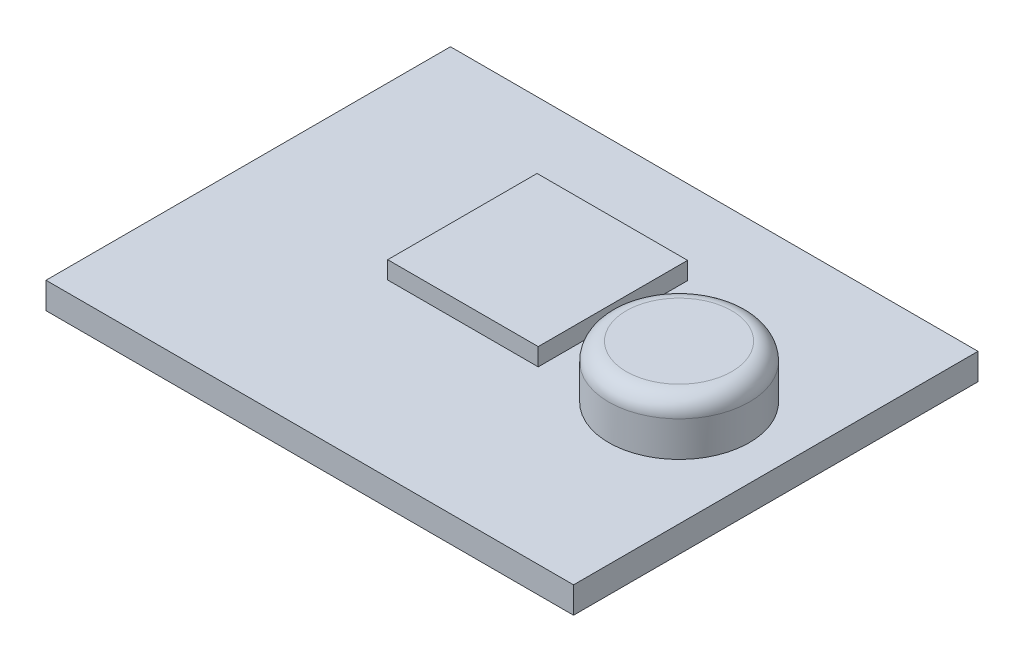
SolidWorks part; units mm, degrees
ref_plane "Plano frontal" through (0, 0, 0) normal (0, 0, 1) x (1, 0, 0)
ref_plane "Plano superior" through (0, 0, 0) normal (0, 1, 0) x (1, 0, 0)
ref_plane "Plano direito" through (0, 0, 0) normal (1, 0, 0) x (0, 0, -1)
sketch "Esboço1" plane through (0, 0, 0) normal (0, 1, 0) x (1, 0, 0)
  line L1 (0, 0) -> (30, 0)
  line L2 (0, 0) -> (0, 23)
  line L3 (0, 23) -> (30, 23)
  line L4 (30, 0) -> (30, 23)
  dimension "D1" = 30
  dimension "D2" = 23
extrude "Ressalto-extrusão1" add sketch "Esboço1" along normal blind 1.5
sketch "Esboço2" plane through (0, 1.5, 0) normal (0, 1, 0) x (-1, 0, 0)
  line L1 (-9.7042, -18.2225) -> (-18.2624, -18.2225)
  line L2 (-9.7042, -18.2225) -> (-9.7042, -9.7279)
  line L3 (-9.7042, -9.7279) -> (-18.2624, -9.7279)
  line L4 (-18.2624, -18.2225) -> (-18.2624, -9.7279)
extrude "Ressalto-extrusão2" add sketch "Esboço2" along normal blind 1
sketch "Esboço3" plane through (0, 1.5, 0) normal (0, 1, 0) x (1, 0, 0)
  line L0 (30, 0) -> (30, 23) construction
  line L1 (30, 23) -> (0, 23) construction
  circle A0 centre (24, 12) radius 4
  dimension "D2" = 8
  dimension "D1" = 6
  dimension "D3" = 11
extrude "Ressalto-extrusão3" add sketch "Esboço3" along normal blind 3
fillet "Filete1" radius 1 1 edges at (24, 4.5, -8)
